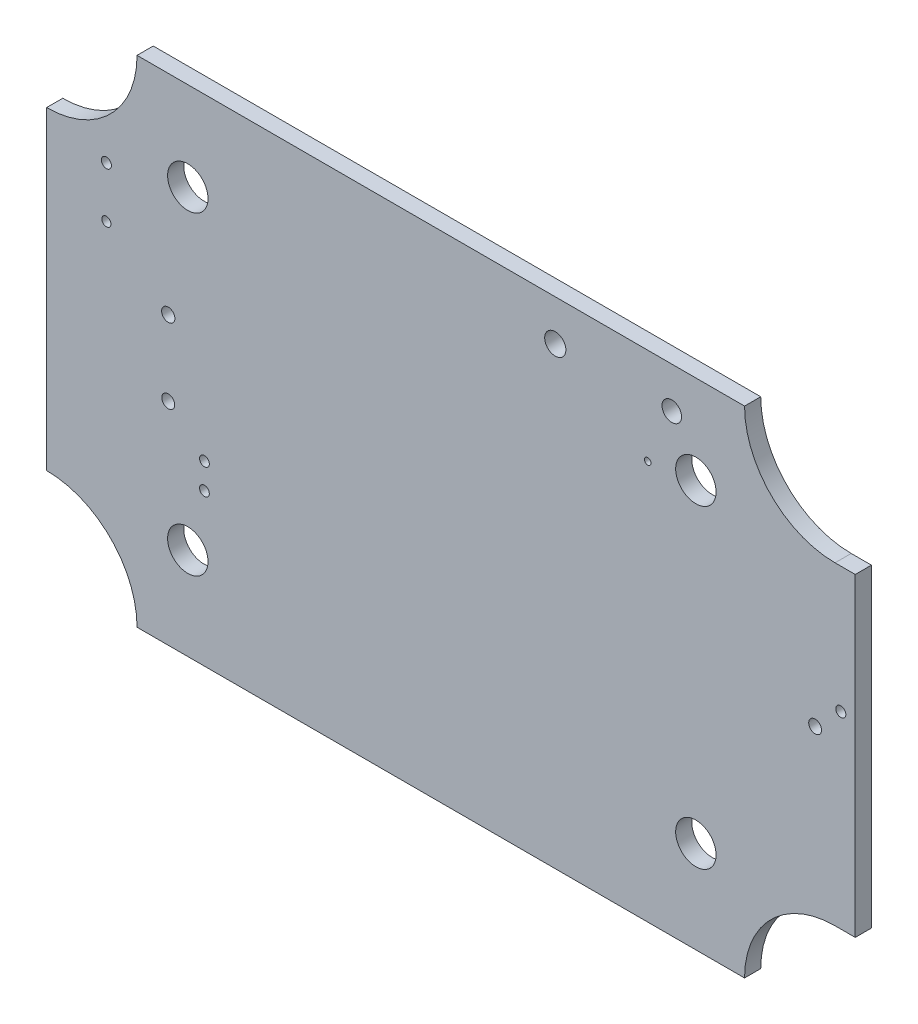
SolidWorks part; units mm, degrees
ref_plane "Front Plane" through (0, 0, 0) normal (0, 0, 1) x (1, 0, 0)
ref_plane "Top Plane" through (0, 0, 0) normal (0, 1, 0) x (1, 0, 0)
ref_plane "Right Plane" through (0, 0, 0) normal (1, 0, 0) x (0, 0, -1)
sketch "Sketch1" plane through (0, 0, 0) normal (0, 0, 1) x (1, 0, 0)
  line L1 (-39, 24.5) -> (39, 24.5)
  line L2 (-39, 24.5) -> (-39, -24.5)
  line L3 (-39, -24.5) -> (39, -24.5)
  line L4 (39, 24.5) -> (39, -24.5)
  line L5 (-39, 24.5) -> (39, -24.5) construction
  line L6 (-39, -24.5) -> (39, 24.5) construction
  point P0 (0, 0)
  dimension "D1" = 49
  dimension "D2" = 78
extrude "Boss-Extrude1" add sketch "Sketch1" along normal blind 1.6
sketch "Sketch2" plane through (0, 0, 1.6) normal (0, 0, 1) x (1, 0, 0)
  circle A0 centre (39, 24.5) radius 8.9512
  circle A1 centre (39, -24.5) radius 8.9512
  circle A2 centre (-39, 24.5) radius 8.9512
  circle A3 centre (-39, -24.5) radius 8.9512
extrude "Cut-Extrude1" cut sketch "Sketch2" against normal blind 10
sketch "Sketch4" plane through (39, 0, 0) normal (1, 0, 0) x (0, 0, -1)
  line L1 (-1.6, 15.5488) -> (0, 15.5488)
  line L2 (-1.6, 15.5488) -> (-1.6, -15.5488)
  line L3 (-1.6, -15.5488) -> (0, -15.5488)
  line L4 (0, 15.5488) -> (0, -15.5488)
extrude "Boss-Extrude3" add sketch "Sketch4" along normal blind 2
sketch "Sketch5" plane through (0, 0, 0) normal (0, 0, -1) x (-1, 0, 0)
  circle A44 centre (-22.8509, 20.4633) radius 0.9681
  circle A45 centre (-11.3235, 20.4633) radius 1.0488
  circle A46 centre (-20.4697, 14.9793) radius 0.3242
  circle A47 centre (26.9637, -3.5963) radius 0.6407
  circle A48 centre (26.9637, 3.8205) radius 0.6552
  circle A49 centre (33.0839, 8.7446) radius 0.4538
  circle A50 centre (33.0839, 13.7784) radius 0.5
  circle A51 centre (23.3834, -9.4806) radius 0.4826
  circle A52 centre (23.3834, -6.9406) radius 0.4826
  circle A53 centre (-39.5709, 3.0818) radius 0.5
  circle A54 centre (-37.0309, 0.5418) radius 0.635
  point P0 (0, 0)
extrude "Cut-Extrude2" cut sketch "Sketch5" against normal blind 10
sketch "Sketch6" plane through (0, 0, 1.6) normal (0, 0, 1) x (1, 0, 0)
  circle A4 centre (25.2329, -15.3766) radius 2
  circle A5 centre (-25.028, -15.3766) radius 2
  circle A6 centre (-25.028, 15.721) radius 2
  circle A7 centre (25.2329, 15.721) radius 2
  point P15 (-24.4938, -15.3766)
  point P17 (-24.4938, 15.721)
  point P19 (24.6488, 15.721)
extrude "Cut-Extrude3" cut sketch "Sketch6" against normal blind 10
